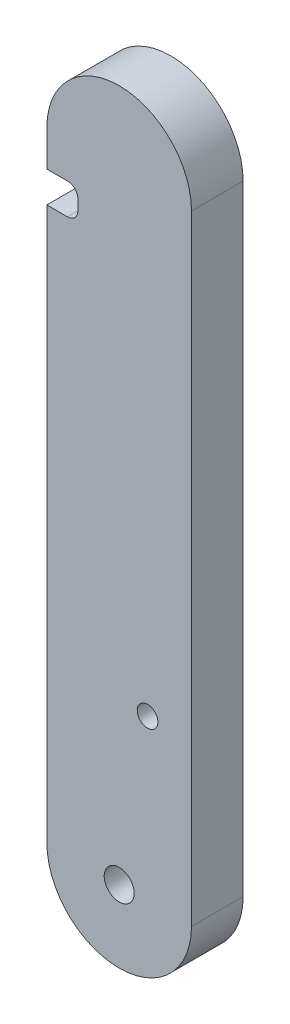
SolidWorks part; units mm, degrees
ref_plane "Front Plane" through (0, 0, 0) normal (0, 0, 1) x (1, 0, 0)
ref_plane "Top Plane" through (0, 0, 0) normal (0, 1, 0) x (1, 0, 0)
ref_plane "Right Plane" through (0, 0, 0) normal (1, 0, 0) x (0, 0, -1)
sketch "Sketch1" plane through (0, 0, 0) normal (0, 0, 1) x (1, 0, 0)
  line L0 (-15.5, -15.5) -> (-15.5, 44.5) construction
  line L1 (-22.5, -15.5) -> (-22.5, 44.5)
  line L2 (-8.5, -15.5) -> (-8.5, 44.5)
  circle A0 centre (-15.5, -15.5) radius 1.5
  arc A1 (-22.5, -15.5) -> (-8.5, -15.5) centre (-15.5, -15.5) ccw
  arc A2 (-8.5, 44.5) -> (-22.5, 44.5) centre (-15.5, 44.5) ccw
  point P3 (-15.5, 14.5)
  dimension "D1" = 7
  dimension "D2" = 60
  dimension "D3" = 3
extrude "Boss-Extrude1" add sketch "Sketch1" along normal blind 5 contours L1 A2 L2 A1
sketch "Sketch2" plane through (0, 0, 5) normal (0, 0, 1) x (1, 0, 0)
  circle A0 centre (-12.75, 0) radius 1
  dimension "D1" = 2
extrude "Cut-Extrude1" cut sketch "Sketch2" against normal blind 5
sketch "Sketch3" plane through (0, 0, 5) normal (0, 0, 1) x (1, 0, 0)
  line L0 (-22.5, -15.5) -> (-22.5, 44.5) construction
  line L1 (-19.5, 41) -> (-22.5, 41)
  line L2 (-19.5, 41) -> (-19.5, 38)
  line L3 (-19.5, 38) -> (-22.5, 38)
  line L4 (-22.5, 41) -> (-22.5, 38)
  line L5 (-19.5, 41) -> (-22.5, 38) construction
  line L6 (-19.5, 38) -> (-22.5, 41) construction
  circle A0 centre (-15.5, -15.5) radius 1.2295 construction
  point P0 (-21, 39.5)
  dimension "D2" = 55
  dimension "D1" = 3
  dimension "D3" = 3
extrude "Cut-Extrude2" cut sketch "Sketch3" against normal blind 5
fillet "Fillet1" radius 1 2 edges at (-19.5, 38, 2.5) (-19.5, 41, 2.5)
sketch "Sketch4" plane through (0, 0, 5) normal (0, 0, 1) x (1, 0, 0)
  circle A0 centre (-15.5, -15.5) radius 1.45
  dimension "D1" = 2.9
extrude "Cut-Extrude3" cut sketch "Sketch4" against normal blind 5
